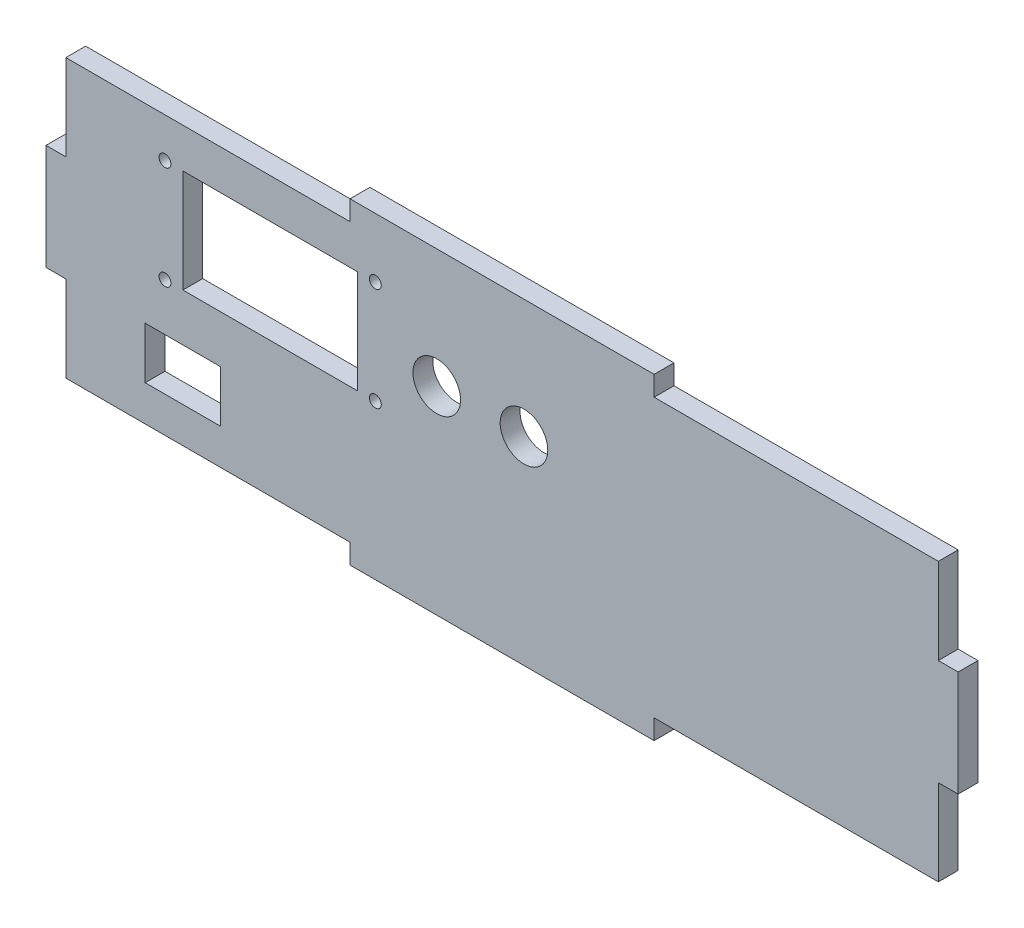
SolidWorks part; units mm, degrees
ref_plane "Alzado" through (0, 0, 0) normal (0, 0, 1) x (1, 0, 0)
ref_plane "Planta" through (0, 0, 0) normal (0, 1, 0) x (1, 0, 0)
ref_plane "Vista lateral" through (0, 0, 0) normal (1, 0, 0) x (0, 0, -1)
sketch "Croquis1" plane through (0, 0, 0) normal (0, 0, 1) x (1, 0, 0)
  line L0 (30, 65) -> (83.04, 65) construction
  line L1 (0, 0) -> (230, 0)
  line L2 (0, 0) -> (0, 80)
  line L3 (0, 80) -> (230, 80)
  line L4 (230, 0) -> (230, 80)
  line L5 (83.04, 65) -> (83.04, 39) construction
  line L6 (83.04, 39) -> (30, 39) construction
  line L7 (30, 39) -> (30, 65) construction
  line L8 (0, 40) -> (-6.7015, 40) construction
  line L9 (0, 53.3333) -> (5, 53.3333)
  line L10 (0, 53.3333) -> (0, 26.6667)
  line L11 (0, 26.6667) -> (5, 26.6667)
  line L12 (5, 53.3333) -> (5, 26.6667)
  line L13 (76.6667, 80) -> (153.3333, 80)
  line L14 (76.6667, 80) -> (76.6667, 75)
  line L15 (76.6667, 75) -> (153.3333, 75)
  line L16 (153.3333, 80) -> (153.3333, 75)
  line L17 (115, 80) -> (115, 87.6964) construction
  line L18 (230, 26.6667) -> (225, 26.6667)
  line L19 (230, 53.3333) -> (225, 53.3333)
  line L20 (225, 53.3333) -> (225, 26.6667)
  line L21 (153.3333, 0) -> (153.3333, 5)
  line L22 (76.6667, 0) -> (76.6667, 5)
  line L23 (76.6667, 5) -> (153.3333, 5)
  line L24 (56.52, 65) -> (56.52, 39) construction
  line L25 (30, 52) -> (83.04, 52) construction
  line L26 (76.6667, 75) -> (0, 75)
  line L27 (34.52, 65) -> (78.52, 65)
  line L28 (34.52, 65) -> (34.52, 39)
  line L29 (34.52, 39) -> (78.52, 39)
  line L30 (78.52, 65) -> (78.52, 39)
  line L31 (34.52, 65) -> (78.52, 39) construction
  line L32 (34.52, 39) -> (78.52, 65) construction
  line L33 (153.3333, 75) -> (230, 75)
  line L34 (5, 0) -> (5, 80)
  line L35 (0, 5) -> (230, 5)
  line L36 (225, 0) -> (225, 80)
  circle A0 centre (30, 65) radius 1.5
  circle A1 centre (83.04, 65) radius 1.5
  circle A2 centre (30, 39) radius 1.5
  circle A3 centre (83.04, 39) radius 1.5
  point P37 (56.52, 52)
  dimension "D3" = 3
  dimension "D1" = 80
  dimension "D2" = 230
  dimension "D4" = 53.04
  dimension "D5" = 26
  dimension "D6" = 30
  dimension "D7" = 15
  dimension "D8" = 26.6667
  dimension "D9" = 26.6667
  dimension "D10" = 76.6667
  dimension "D11" = 76.6667
  dimension "D12" = 5
  dimension "D13" = 5
  dimension "D15" = 26
  dimension "D14" = 44
extrude "Saliente-Extruir1" add sketch "Croquis1" along normal blind 5 contours L35 L36 L20 L33 L15 L26 L34 L12 L23 A3 A2 A1 A0 L27 L30 L29 L28 | L19 L20 L18 L4 | L23 L22 L1 L21 | L12 L9 L2 L11 | L16 L3 L14 L15
sketch "Croquis2" plane through (0, 0, 5) normal (0, 0, 1) x (1, 0, 0)
  line L0 (96.6667, 20) -> (116.6667, 20) construction
  line L3 (116.6667, 20) -> (136.6667, 20) construction
  line L5 (76.6667, 0) -> (76.6667, 5) construction
  line L6 (153.3333, 5) -> (225, 5) construction
  circle A0 centre (96.6667, 20) radius 4.15
  circle A1 centre (116.6667, 20) radius 4.15
  circle A2 centre (136.6667, 20) radius 4.15
  point P4 (126.6667, 20)
  dimension "D1" = 8.3
  dimension "D2" = 15
  dimension "D3" = 20
  dimension "D4" = 20
  dimension "D5" = 20
extrude "Cortar-Extruir1" cut sketch "Croquis2" against normal blind 10
sketch "Croquis3" plane through (0, 0, 5) normal (0, 0, 1) x (1, 0, 0)
  line L0 (34.52, 39) -> (78.52, 39) construction
  line L1 (25, 27) -> (44, 27)
  line L2 (25, 27) -> (25, 14)
  line L3 (25, 14) -> (44, 14)
  line L4 (44, 27) -> (44, 14)
  line L6 (5, 5) -> (5, 26.6667) construction
  dimension "D1" = 19
  dimension "D2" = 13
  dimension "D3" = 12
  dimension "D4" = 20
extrude "Cortar-Extruir2" cut sketch "Croquis3" against normal blind 10
sketch "Croquis4" plane through (0, 0, 5) normal (0, 0, 1) x (1, 0, 0)
  line L0 (65, 20) -> (80, 20) construction
  line L3 (5, 53.3333) -> (5, 75) construction
  line L4 (5, 5) -> (76.6667, 5) construction
  circle A0 centre (65, 20) radius 4.15
  circle A1 centre (80, 20) radius 4.15
  dimension "D1" = 8.3
  dimension "D4" = 15
  dimension "D2" = 15
  dimension "D3" = 60
extrude "Cortar-Extruir3" cut sketch "Croquis4" against normal blind 10
sketch "Croquis5" plane through (0, 0, 5) normal (0, 0, 1) x (1, 0, 0)
  line L0 (98.52, 50) -> (120.52, 50) construction
  line L1 (34.52, 65) -> (78.52, 65) construction
  line L2 (78.52, 65) -> (78.52, 39) construction
  circle A0 centre (98.52, 50) radius 6
  circle A1 centre (120.52, 50) radius 6
  dimension "D1" = 12
  dimension "D2" = 12
  dimension "D3" = 22
  dimension "D4" = 15
  dimension "D5" = 20
extrude "Cortar-Extruir4" cut sketch "Croquis5" against normal blind 10
sketch "Croquis6" plane through (0, 0, 5) normal (0, 0, 1) x (1, 0, 0)
  line L0 (44, 14) -> (44, 27) construction
  line L1 (25, 14) -> (44, 14) construction
  line L2 (44, 27) -> (25, 27) construction
  line L3 (25, 27) -> (25, 14) construction
  line L4 (34.52, 39) -> (78.52, 39) construction
  line L5 (34.52, 65) -> (34.52, 39) construction
  line L6 (34.52, 65) -> (78.52, 65) construction
  line L7 (78.52, 65) -> (78.52, 39) construction
  line L8 (44, 14) -> (44, 27)
  line L9 (25, 14) -> (44, 14)
  line L10 (44, 27) -> (25, 27)
  line L11 (25, 27) -> (25, 14)
  line L12 (34.52, 39) -> (78.52, 39)
  line L13 (34.52, 65) -> (34.52, 39)
  line L14 (34.52, 65) -> (78.52, 65)
  line L15 (78.52, 65) -> (78.52, 39)
  line L20 (5, 5) -> (76.6667, 5)
  line L21 (76.6667, 5) -> (76.6667, 0)
  line L22 (76.6667, 0) -> (153.3333, 0)
  line L23 (153.3333, 0) -> (153.3333, 5)
  line L24 (153.3333, 5) -> (225, 5)
  line L25 (225, 5) -> (225, 26.6667)
  line L26 (225, 26.6667) -> (230, 26.6667)
  line L27 (230, 26.6667) -> (230, 53.3333)
  line L28 (230, 53.3333) -> (225, 53.3333)
  line L29 (225, 53.3333) -> (225, 75)
  line L30 (225, 75) -> (153.3333, 75)
  line L31 (153.3333, 75) -> (153.3333, 80)
  line L32 (153.3333, 80) -> (76.6667, 80)
  line L33 (76.6667, 80) -> (76.6667, 75)
  line L34 (76.6667, 75) -> (5, 75)
  line L35 (5, 75) -> (5, 53.3333)
  line L36 (5, 53.3333) -> (0, 53.3333)
  line L37 (0, 53.3333) -> (0, 26.6667)
  line L38 (0, 26.6667) -> (5, 26.6667)
  line L39 (5, 26.6667) -> (5, 5)
  line L40 (5, 5) -> (76.6667, 5)
  line L41 (76.6667, 5) -> (76.6667, 0)
  line L42 (76.6667, 0) -> (153.3333, 0)
  line L43 (153.3333, 0) -> (153.3333, 5)
  line L44 (153.3333, 5) -> (225, 5)
  line L45 (225, 5) -> (225, 26.6667)
  line L46 (225, 26.6667) -> (230, 26.6667)
  line L47 (230, 26.6667) -> (230, 53.3333)
  line L48 (230, 53.3333) -> (225, 53.3333)
  line L49 (225, 53.3333) -> (225, 75)
  line L50 (225, 75) -> (153.3333, 75)
  line L51 (153.3333, 75) -> (153.3333, 80)
  line L52 (153.3333, 80) -> (76.6667, 80)
  line L53 (76.6667, 80) -> (76.6667, 75)
  line L54 (76.6667, 75) -> (5, 75)
  line L55 (5, 75) -> (5, 53.3333)
  line L56 (5, 53.3333) -> (0, 53.3333)
  line L57 (0, 53.3333) -> (0, 26.6667)
  line L58 (0, 26.6667) -> (5, 26.6667)
  line L59 (5, 26.6667) -> (5, 5)
  circle A0 centre (98.52, 50) radius 6 construction
  circle A1 centre (120.52, 50) radius 6 construction
  circle A2 centre (136.6667, 20) radius 4.15 construction
  circle A3 centre (116.6667, 20) radius 4.15 construction
  circle A4 centre (96.6667, 20) radius 4.15 construction
  circle A5 centre (80, 20) radius 4.15 construction
  circle A6 centre (65, 20) radius 4.15 construction
  circle A7 centre (83.04, 65) radius 1.5 construction
  circle A8 centre (83.04, 39) radius 1.5 construction
  circle A9 centre (30, 39) radius 1.5 construction
  circle A10 centre (30, 65) radius 1.5 construction
  circle A11 centre (98.52, 50) radius 6
  circle A12 centre (120.52, 50) radius 6
  circle A13 centre (136.6667, 20) radius 4.15
  circle A14 centre (116.6667, 20) radius 4.15
  circle A15 centre (96.6667, 20) radius 4.15
  circle A16 centre (80, 20) radius 4.15
  circle A17 centre (65, 20) radius 4.15
  circle A18 centre (83.04, 65) radius 1.5
  circle A19 centre (83.04, 39) radius 1.5
  circle A20 centre (30, 39) radius 1.5
  circle A21 centre (30, 65) radius 1.5
  dimension "D1" = 0
sketch "Croquis7" plane through (0, 0, 5) normal (0, 0, 1) x (1, 0, 0)
  line L1 (56.7187, 27.329) -> (144.6768, 27.329)
  line L2 (56.7187, 27.329) -> (56.7187, 12.6149)
  line L3 (56.7187, 12.6149) -> (144.6768, 12.6149)
  line L4 (144.6768, 27.329) -> (144.6768, 12.6149)
extrude "Saliente-Extruir2" add sketch "Croquis7" against normal up to surface (5 mm away) up to face at (126.52, 50, 0)
